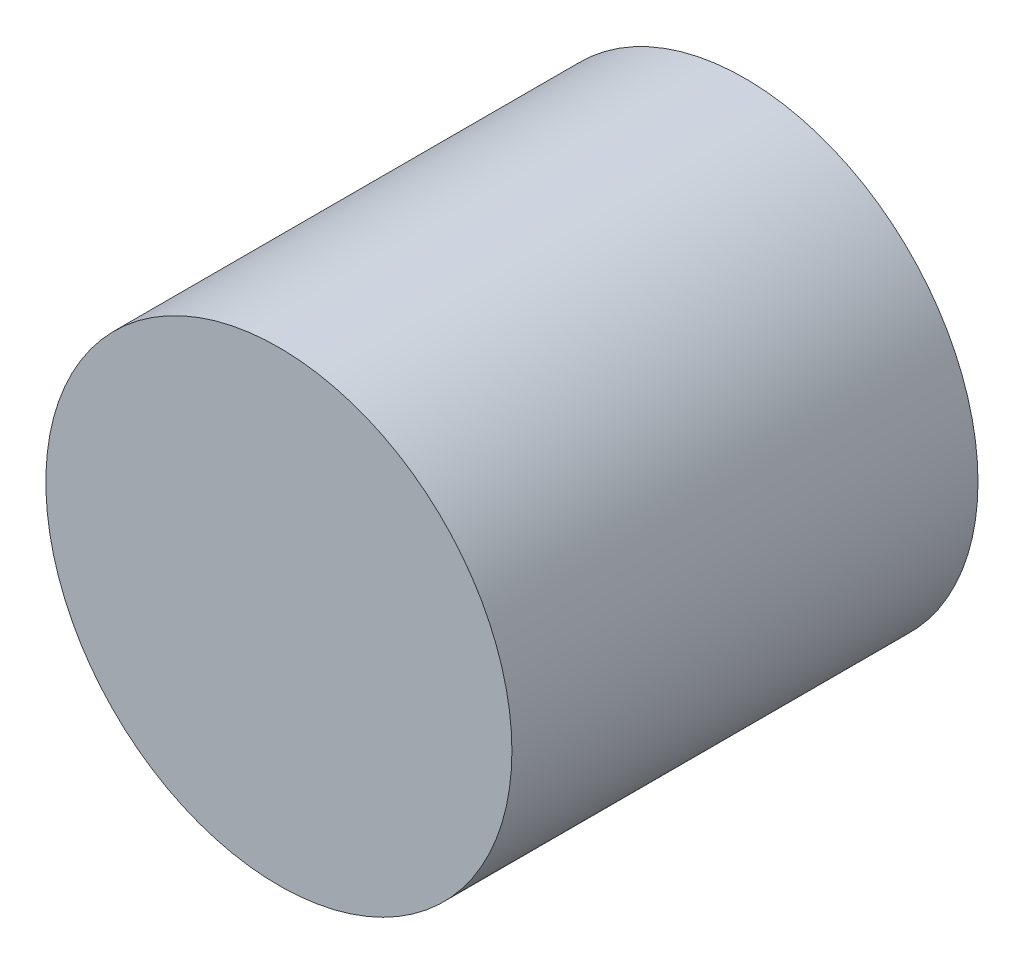
SolidWorks part; units mm, degrees
ref_plane "Front Plane" through (0, 0, 0) normal (0, 0, 1) x (1, 0, 0)
ref_plane "Top Plane" through (0, 0, 0) normal (0, 1, 0) x (1, 0, 0)
ref_plane "Right Plane" through (0, 0, 0) normal (1, 0, 0) x (0, 0, -1)
sketch "Sketch1" plane through (0, 0, 0) normal (0, 0, 1) x (1, 0, 0)
  circle A0 centre (0, 0) radius 1.75
  dimension "D1" = 3.5
extrude "Boss-Extrude1" add sketch "Sketch1" along normal blind 3.5
